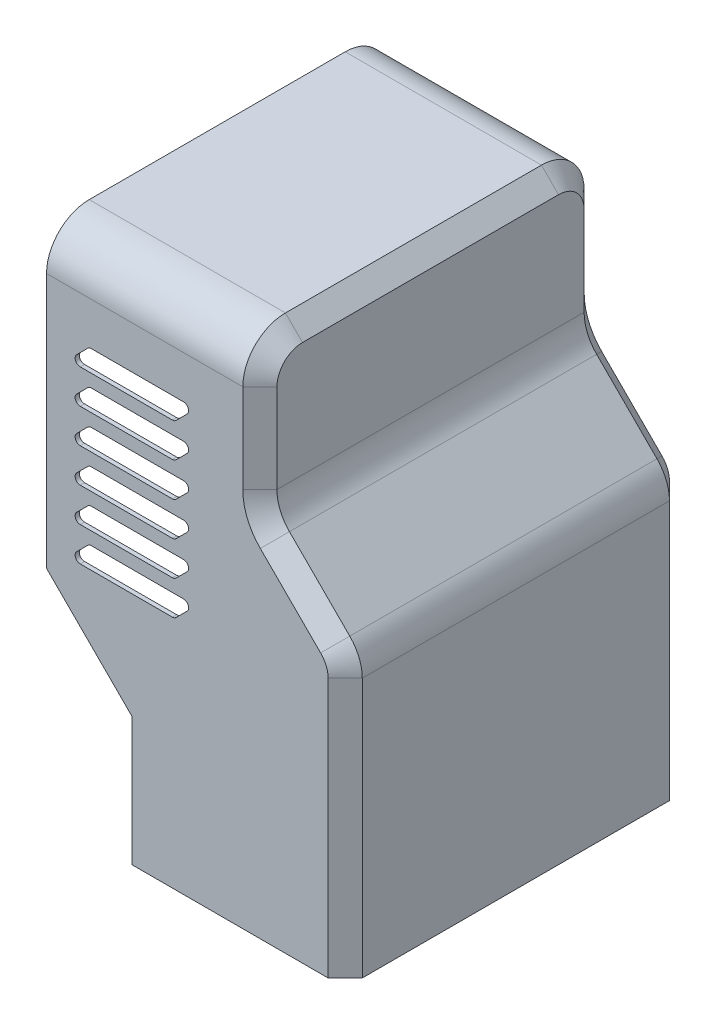
SolidWorks part; units mm, degrees
ref_plane "Front Plane" through (0, 0, 0) normal (0, 0, 1) x (1, 0, 0)
ref_plane "Top Plane" through (0, 0, 0) normal (0, 1, 0) x (1, 0, 0)
ref_plane "Right Plane" through (0, 0, 0) normal (1, 0, 0) x (0, 0, -1)
sketch "Sketch1" plane through (0, 0, 0) normal (0, 0, 1) x (1, 0, 0)
  line L8 (0, 0) -> (63.5, 0)
  line L9 (63.5, 0) -> (63.5, 82.55)
  line L10 (63.5, 82.55) -> (38.1, 107.95)
  line L11 (38.1, 107.95) -> (38.1, 152.4)
  line L12 (38.1, 152.4) -> (-25.4, 152.4)
  line L13 (-25.4, 152.4) -> (-25.4, 63.6869)
  line L14 (-25.4, 63.6869) -> (0, 38.2869)
  line L15 (0, 38.2869) -> (0, 0)
  dimension "D1" = 63.5
  dimension "D2" = 63.5
  dimension "D3" = 152.4
  dimension "D4" = 45
  dimension "D5" = 69.85
  dimension "D6" = 44.45
  dimension "D7" = 76.2
extrude "Boss-Extrude1" add sketch "Sketch1" along normal mid plane 101.6
fillet "Fillet1" radius 12.7 4 edges at (63.5, 82.55, 0) (38.1, 107.95, 0) (6.35, 152.4, -50.8) (6.35, 152.4, 50.8)
chamfer "Chamfer1" distance 5.08 angle 45 13 edges at (63.5, 38.6447, 50.8) (63.5, 38.6447, -50.8) (62.5333, 82.1496, 50.8) (62.5333, 82.1496, -50.8) (50.8, 95.25, 50.8) (50.8, 95.25, -50.8) (39.0667, 108.3504, 50.8) (39.0667, 108.3504, -50.8) (38.1, 126.4553, 50.8) (38.1, 126.4553, -50.8) (38.1, 148.6803, 47.0803) (38.1, 148.6803, -47.0803) (38.1, 152.4, 0)
shell "Shell1" thickness 1.27
sketch "Sketch2" plane through (0, 0, 50.8) normal (0, 0, 1) x (1, 0, 0)
  line L0 (-13.1464, 126.5536) -> (-16.4484, 123.2516)
  line L1 (-12.0687, 127) -> (15.3707, 127)
  line L2 (-15.3707, 120.65) -> (12.0687, 120.65)
  line L3 (16.4484, 124.3984) -> (13.1464, 121.0964)
  line L4 (-25.4, 139.7) -> (-25.4, 63.6869) construction
  line L5 (-25.4, 152.4) -> (33.02, 152.4) construction
  line L6 (-13.1464, 116.3936) -> (-16.4484, 113.0916)
  line L7 (-12.0687, 116.84) -> (15.3707, 116.84)
  line L8 (-15.3707, 110.49) -> (12.0687, 110.49)
  line L9 (16.4484, 114.2384) -> (13.1464, 110.9364)
  line L10 (-13.1464, 106.2336) -> (-16.4484, 102.9316)
  line L11 (-12.0687, 106.68) -> (15.3707, 106.68)
  line L12 (-15.3707, 100.33) -> (12.0687, 100.33)
  line L13 (16.4484, 104.0784) -> (13.1464, 100.7764)
  line L14 (-13.1464, 96.0736) -> (-16.4484, 92.7716)
  line L15 (-12.0687, 96.52) -> (15.3707, 96.52)
  line L16 (-15.3707, 90.17) -> (12.0687, 90.17)
  line L17 (16.4484, 93.9184) -> (13.1464, 90.6164)
  line L18 (-13.1464, 85.9136) -> (-16.4484, 82.6116)
  line L19 (-12.0687, 86.36) -> (15.3707, 86.36)
  line L20 (-15.3707, 80.01) -> (12.0687, 80.01)
  line L21 (16.4484, 83.7584) -> (13.1464, 80.4564)
  line L22 (-13.1464, 75.7536) -> (-16.4484, 72.4516)
  line L23 (-12.0687, 76.2) -> (15.3707, 76.2)
  line L24 (-15.3707, 69.85) -> (12.0687, 69.85)
  line L25 (16.4484, 73.5984) -> (13.1464, 70.2964)
  line L26 (-13.1464, 126.5536) -> (-13.1464, 116.3936) construction
  arc A0 (15.3707, 127) -> (16.4484, 124.3984) centre (15.3707, 125.476) cw
  arc A1 (12.0687, 120.65) -> (13.1464, 121.0964) centre (12.0687, 122.174) ccw
  arc A2 (-12.0687, 127) -> (-13.1464, 126.5536) centre (-12.0687, 125.476) ccw
  arc A3 (-16.4484, 123.2516) -> (-15.3707, 120.65) centre (-15.3707, 122.174) ccw
  arc A4 (15.3707, 116.84) -> (16.4484, 114.2384) centre (15.3707, 115.316) cw
  arc A5 (12.0687, 110.49) -> (13.1464, 110.9364) centre (12.0687, 112.014) ccw
  arc A6 (-12.0687, 116.84) -> (-13.1464, 116.3936) centre (-12.0687, 115.316) ccw
  arc A7 (-16.4484, 113.0916) -> (-15.3707, 110.49) centre (-15.3707, 112.014) ccw
  arc A8 (15.3707, 106.68) -> (16.4484, 104.0784) centre (15.3707, 105.156) cw
  arc A9 (12.0687, 100.33) -> (13.1464, 100.7764) centre (12.0687, 101.854) ccw
  arc A10 (-12.0687, 106.68) -> (-13.1464, 106.2336) centre (-12.0687, 105.156) ccw
  arc A11 (-16.4484, 102.9316) -> (-15.3707, 100.33) centre (-15.3707, 101.854) ccw
  arc A12 (15.3707, 96.52) -> (16.4484, 93.9184) centre (15.3707, 94.996) cw
  arc A13 (12.0687, 90.17) -> (13.1464, 90.6164) centre (12.0687, 91.694) ccw
  arc A14 (-12.0687, 96.52) -> (-13.1464, 96.0736) centre (-12.0687, 94.996) ccw
  arc A15 (-16.4484, 92.7716) -> (-15.3707, 90.17) centre (-15.3707, 91.694) ccw
  arc A16 (15.3707, 86.36) -> (16.4484, 83.7584) centre (15.3707, 84.836) cw
  arc A17 (12.0687, 80.01) -> (13.1464, 80.4564) centre (12.0687, 81.534) ccw
  arc A18 (-12.0687, 86.36) -> (-13.1464, 85.9136) centre (-12.0687, 84.836) ccw
  arc A19 (-16.4484, 82.6116) -> (-15.3707, 80.01) centre (-15.3707, 81.534) ccw
  arc A20 (15.3707, 76.2) -> (16.4484, 73.5984) centre (15.3707, 74.676) cw
  arc A21 (12.0687, 69.85) -> (13.1464, 70.2964) centre (12.0687, 71.374) ccw
  arc A22 (-12.0687, 76.2) -> (-13.1464, 75.7536) centre (-12.0687, 74.676) ccw
  arc A23 (-16.4484, 72.4516) -> (-15.3707, 69.85) centre (-15.3707, 71.374) ccw
  point P10 (19.05, 127)
  point P17 (-19.05, 120.65)
  dimension "D6" = 1.524
  dimension "D1" = 6.35
  dimension "D2" = 25.4
  dimension "D3" = 38.1
  dimension "D4" = 45
  dimension "D5" = 6.35
  dimension "D8" = 10.16
  dimension "D7" = 6
extrude "Cut-Extrude1" cut sketch "Sketch2" against normal through all
